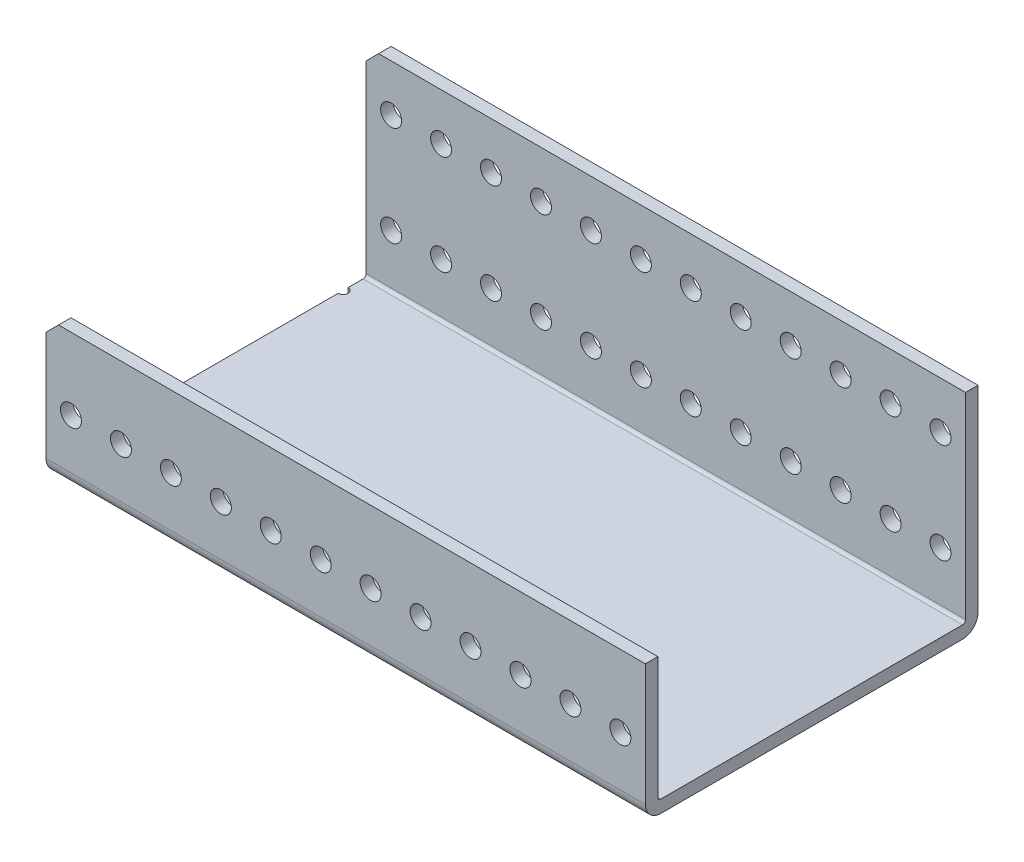
SolidWorks part; units mm, degrees
ref_plane "Front Plane" through (0, 0, 0) normal (0, 0, 1) x (1, 0, 0)
ref_plane "Top Plane" through (0, 0, 0) normal (0, 1, 0) x (1, 0, 0)
ref_plane "Right Plane" through (0, 0, 0) normal (1, 0, 0) x (0, 0, -1)
ref_plane "Plane4" through (0, 57.8164, 0) normal (0, 1, 0) x (1, 0, 0)
sketch "Sketch1" plane through (0, 57.8164, 0) normal (0, 1, 0) x (1, 0, 0)
  line L0 (602.398, -145.5605) -> (602.398, -60.9785)
  line L1 (602.398, -60.9785) -> (-96.102, -60.9785)
  line L2 (-96.102, -60.9785) -> (-96.102, -145.5605)
  line L3 (-96.102, -145.5605) -> (602.398, -145.5605)
  dimension "D1" = 698.5
extrude "Boss-Extrude1" add sketch "Sketch1" against normal blind 34.925
sketch "Sketch2" plane through (602.398, 0, 0) normal (1, 0, 0) x (0, 0, -1)
  line L0 (-60.9785, 57.8164) -> (-142.3855, 57.8164)
  line L1 (-142.3855, 57.8164) -> (-142.3855, 26.0664)
  line L2 (-142.3855, 26.0664) -> (-60.9785, 26.0664)
  line L3 (-60.9785, 26.0664) -> (-60.9785, 57.8164)
extrude "Cut-Extrude1" cut sketch "Sketch2" against normal through all
sketch "Sketch3" plane through (0, 26.0664, 0) normal (0, 1, 0) x (-1, 0, 0)
  line L0 (96.102, 60.9785) -> (-602.398, 60.9785)
  line L1 (-602.398, 60.9785) -> (-602.398, 64.1535)
  line L2 (-602.398, 64.1535) -> (96.102, 64.1535)
  line L3 (96.102, 64.1535) -> (96.102, 60.9785)
  line L5 (-602.398, 142.3855) -> (-602.398, 60.9785) construction
  line L6 (96.102, 142.3855) -> (96.102, 60.9785) construction
extrude "Boss-Extrude2" add sketch "Sketch3" along normal blind 50.8
hole_wizard "M2 Clearance Hole1" positions "Sketch5" profile "Sketch4" hole size "M2" standard "ANSI Metric" end condition through all
sketch "Sketch5" plane through (0, 26.0664, 0) normal (0, 1, 0) x (1, 0, 0)
  point P0 (-96.102, -136.5435)
  point P1 (-96.102, -69.9955)
sketch "Sketch4" plane through (-96.102, 26.0664, 136.5435) normal (1, 0, 0) x (0, 0, 1)
  line L0 (0, 0) -> (0, 3.175)
  line L1 (0, 3.175) -> (1.27, 3.175)
  line L2 (1.27, 3.175) -> (1.27, 0)
  line L5 (1.27, 0) -> (0, 0)
  line L11 (0, -6.35) -> (0, 107.95) construction
  dimension "Thru Hole Dia." = 2.54
  dimension "Thru Hole Depth" = 3.175
hole_wizard "M5 Clearance Hole1" positions "Sketch7" profile "Sketch6" hole size "M5" standard "ANSI Metric" end condition through all
sketch "Sketch7" plane through (0, 0, 60.9785) normal (0, 0, -1) x (-1, 0, 0)
  point P0 (-469.048, 64.9284)
  point P1 (-481.748, 64.9284)
  point P2 (-469.048, 39.5284)
  point P3 (-481.748, 39.5284)
  point P4 (-456.348, 39.5284)
  point P5 (-443.648, 39.5284)
  point P6 (-430.948, 39.5284)
  point P7 (-418.248, 39.5284)
  point P8 (-405.548, 39.5284)
  point P9 (-392.848, 39.5284)
  point P10 (-380.148, 39.5284)
  point P11 (-367.448, 39.5284)
  point P12 (-354.748, 39.5284)
  point P13 (-342.048, 39.5284)
  point P14 (-329.348, 39.5284)
  point P15 (-316.648, 39.5284)
  point P16 (-303.948, 39.5284)
  point P17 (-291.248, 39.5284)
  point P18 (-278.548, 39.5284)
  point P19 (-265.848, 39.5284)
  point P20 (-253.148, 39.5284)
  point P21 (-240.448, 39.5284)
  point P22 (-227.748, 39.5284)
  point P23 (-215.048, 39.5284)
  point P24 (-202.348, 39.5284)
  point P25 (-189.648, 39.5284)
  point P26 (-176.948, 39.5284)
  point P27 (-164.248, 39.5284)
  point P28 (-151.548, 39.5284)
  point P29 (-138.848, 39.5284)
  point P30 (-126.148, 39.5284)
  point P31 (-113.448, 39.5284)
  point P32 (-100.748, 39.5284)
  point P33 (-88.048, 39.5284)
  point P34 (-75.348, 39.5284)
  point P35 (-62.648, 39.5284)
  point P36 (-49.948, 39.5284)
  point P37 (-37.248, 39.5284)
  point P38 (-24.548, 39.5284)
  point P39 (-11.848, 39.5284)
  point P40 (0.852, 39.5284)
  point P41 (13.552, 39.5284)
  point P42 (26.252, 39.5284)
  point P43 (38.952, 39.5284)
  point P44 (51.652, 39.5284)
  point P45 (64.352, 39.5284)
  point P46 (77.052, 39.5284)
  point P47 (89.752, 39.5284)
  point P48 (-456.348, 64.9284)
  point P49 (-443.648, 64.9284)
  point P50 (-430.948, 64.9284)
  point P51 (-418.248, 64.9284)
  point P52 (-405.548, 64.9284)
  point P53 (-392.848, 64.9284)
  point P54 (-380.148, 64.9284)
  point P55 (-367.448, 64.9284)
  point P56 (-354.748, 64.9284)
  point P57 (-342.048, 64.9284)
  point P58 (-329.348, 64.9284)
  point P59 (-316.648, 64.9284)
  point P60 (-303.948, 64.9284)
  point P61 (-291.248, 64.9284)
  point P62 (-278.548, 64.9284)
  point P63 (-265.848, 64.9284)
  point P64 (-253.148, 64.9284)
  point P65 (-240.448, 64.9284)
  point P66 (-227.748, 64.9284)
  point P67 (-215.048, 64.9284)
  point P68 (-202.348, 64.9284)
  point P69 (-189.648, 64.9284)
  point P70 (-176.948, 64.9284)
  point P71 (-164.248, 64.9284)
  point P72 (-151.548, 64.9284)
  point P73 (-138.848, 64.9284)
  point P74 (-126.148, 64.9284)
  point P75 (-113.448, 64.9284)
  point P76 (-100.748, 64.9284)
  point P77 (-88.048, 64.9284)
  point P78 (-75.348, 64.9284)
  point P79 (-62.648, 64.9284)
  point P80 (-49.948, 64.9284)
  point P81 (-37.248, 64.9284)
  point P82 (-24.548, 64.9284)
  point P83 (-11.848, 64.9284)
  point P84 (0.852, 64.9284)
  point P85 (13.552, 64.9284)
  point P86 (26.252, 64.9284)
  point P87 (38.952, 64.9284)
  point P88 (51.652, 64.9284)
  point P89 (64.352, 64.9284)
  point P90 (77.052, 64.9284)
  point P91 (89.752, 64.9284)
  point P97 (-494.448, 64.9284)
  point P98 (-494.448, 39.5284)
  point P99 (-507.148, 64.9284)
  point P100 (-507.148, 39.5284)
  point P101 (-519.848, 64.9284)
  point P102 (-519.848, 39.5284)
  point P103 (-532.548, 64.9284)
  point P104 (-532.548, 39.5284)
  point P105 (-545.248, 64.9284)
  point P106 (-545.248, 39.5284)
  point P107 (-557.948, 64.9284)
  point P108 (-557.948, 39.5284)
  point P109 (-570.648, 64.9284)
  point P110 (-570.648, 39.5284)
  point P111 (-583.348, 64.9284)
  point P112 (-583.348, 39.5284)
  point P113 (-596.048, 64.9284)
  point P114 (-596.048, 39.5284)
  dimension "D1" = 10
sketch "Sketch6" plane through (469.048, 64.9284, 60.9785) normal (1, 0, 0) x (0, 1, 0)
  line L0 (0, 0) -> (0, 84.582)
  line L1 (0, 84.582) -> (2.667, 84.582)
  line L2 (2.667, 84.582) -> (2.667, 0)
  line L5 (2.667, 0) -> (0, 0)
  line L11 (0, -6.35) -> (0, 107.95) construction
  dimension "Thru Hole Dia." = 5.334
  dimension "Thru Hole Depth" = 84.582
chamfer "Chamfer1" distance 3.175 angle 45 4 edges at (-96.102, 57.8164, 143.973) (-96.102, 76.8664, 62.566) (602.398, 76.8664, 62.566) (602.398, 57.8164, 143.973)
fillet "Fillet1" radius 0.762 2 edges at (253.148, 26.0664, 64.1535) (253.148, 26.0664, 142.3855)
fillet "Fillet2" radius 3.937 2 edges at (253.148, 22.8914, 145.5605) (253.148, 22.8914, 60.9785)
sketch "Sketch8" plane through (0, 0, 60.9785) normal (0, 0, -1) x (-1, 0, 0)
  line L0 (96.102, 26.8284) -> (96.102, 73.6914) construction
  line L1 (-905.0879, 241.0725) -> (-56.298, 241.0725)
  line L2 (-905.0879, 241.0725) -> (-905.0879, -191.8859)
  line L3 (-905.0879, -191.8859) -> (-56.298, -191.8859)
  line L4 (-56.298, 241.0725) -> (-56.298, -191.8859)
  line L5 (-905.0879, 241.0725) -> (-56.298, -191.8859) construction
  line L6 (-905.0879, -191.8859) -> (-56.298, 241.0725) construction
  point P4 (-480.693, 24.5933)
  dimension "D1" = 152.4
extrude "Cut-Extrude2" cut sketch "Sketch8" against normal through all
